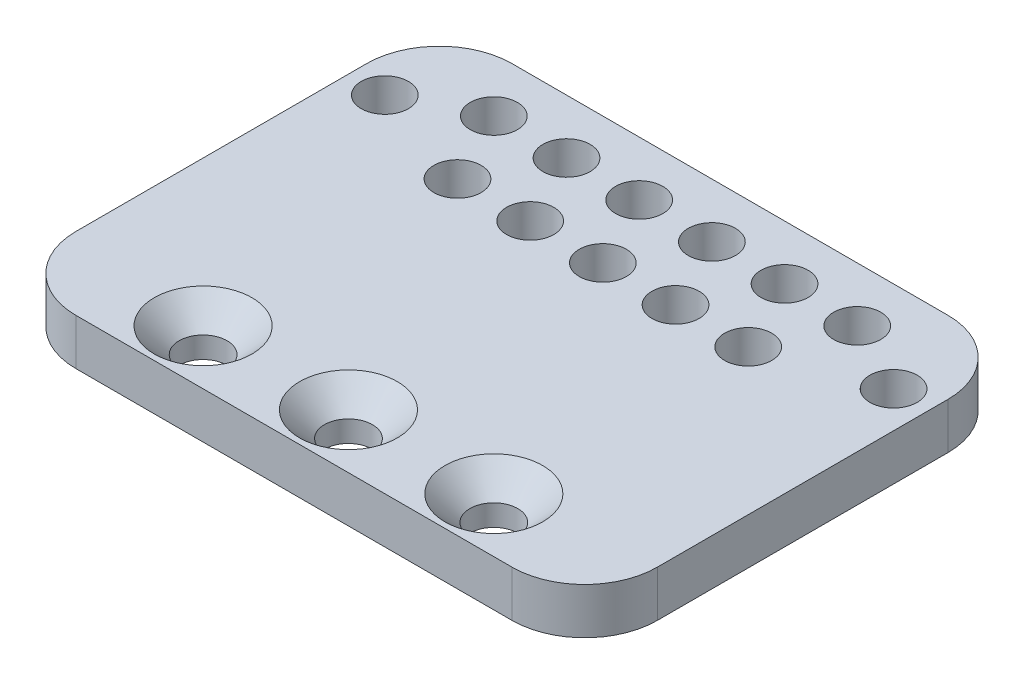
SolidWorks part; units mm, degrees
ref_plane "Front Plane" through (0, 0, 0) normal (0, 0, 1) x (1, 0, 0)
ref_plane "Top Plane" through (0, 0, 0) normal (0, 1, 0) x (1, 0, 0)
ref_plane "Right Plane" through (0, 0, 0) normal (1, 0, 0) x (0, 0, -1)
sketch "Sketch1" plane through (0, 0, 0) normal (0, 1, 0) x (1, 0, 0)
  line L1 (0, 0) -> (80, 0)
  line L2 (0, 0) -> (0, 60)
  line L3 (0, 60) -> (80, 60)
  line L4 (80, 0) -> (80, 60)
  line L5 (0, 0) -> (80, 60) construction
  line L6 (0, 60) -> (80, 0) construction
  line L8 (0, 37.5) -> (80, 37.5) construction
  line L9 (0, 17.5) -> (80, 17.5) construction
  line L10 (35, 52.5) -> (45, 52.5) construction
  line L11 (40, 42.5) -> (40, 52.5) construction
  line L12 (40, 47.5) -> (80, 47.5) construction
  line L13 (40, 47.5) -> (0, 47.5) construction
  circle A0 centre (40, 7.5) radius 3.1
  circle A1 centre (20, 7.5) radius 3.1
  circle A2 centre (60, 7.5) radius 3.1
  circle A5 centre (25, 27.35) radius 3.1 construction
  circle A7 centre (55, 27.35) radius 3.1 construction
  circle A8 centre (35, 52.5) radius 3.25
  circle A9 centre (45, 52.5) radius 3.25
  circle A10 centre (25, 52.5) radius 3.25
  circle A11 centre (30, 42.5) radius 3.25
  circle A12 centre (40, 42.5) radius 3.25
  circle A13 centre (50, 42.5) radius 3.25
  circle A14 centre (20, 42.5) radius 3.25
  circle A15 centre (15, 52.5) radius 3.25
  circle A16 centre (55, 52.5) radius 3.25
  circle A17 centre (65, 52.5) radius 3.25
  circle A18 centre (60, 42.5) radius 3.25
  circle A19 centre (75, 47.5) radius 3.25
  circle A20 centre (5, 47.5) radius 3.25
  point P4 (40, 30)
  point P12 (0, 0)
  point P13 (0, 0)
  point P48 (40, 52.5)
  dimension "D5" = 6.2
  dimension "D7" = 19.85
  dimension "D13" = 6.5
  dimension "D1" = 80
  dimension "D2" = 60
  dimension "D3" = 20
  dimension "D4" = 20
  dimension "D6" = 7.5
  dimension "D8" = 25
  dimension "D9" = 25
  dimension "D10" = 10
  dimension "D11" = 30
  dimension "D12" = 10
  dimension "D14" = 10
  dimension "D15" = 7.5
  dimension "D16" = 10
  dimension "D17" = 10
  dimension "D18" = 10
  dimension "D19" = 10
  dimension "D20" = 10
  dimension "D21" = 10
  dimension "D22" = 10
  dimension "D23" = 10
  dimension "D24" = 5
  dimension "D25" = 5
extrude "Boss-Extrude1" add sketch "Sketch1" along normal blind 6.35
fillet "Fillet1" radius 10 4 edges at (0, 3.175, -60) (80, 3.175, -60) (80, 3.175, 0) (0, 3.175, 0)
hole_wizard "CSK for M6 SFHCS1" positions "Sketch2" profile "Sketch3" countersink size "M6" standard "Autoliv NAM Metric" end condition up to next
sketch "Sketch2" plane through (0, 6.35, 0) normal (0, 1, 0) x (1, 0, 0)
  point P0 (20, 7.5)
  point P3 (40, 7.5)
  point P6 (60, 7.5)
sketch "Sketch3" plane through (20, 6.35, -7.5) normal (1, 0, 0) x (0, 0, 1)
  line L0 (0, 0) -> (0, 6.35)
  line L1 (0, 6.35) -> (3.3, 6.35)
  line L2 (3.3, 6.35) -> (3.3, 3.42)
  line L3 (3.3, 3.42) -> (6.72, 0)
  line L5 (6.72, 0) -> (0, 0)
  line L6 (-3.3, 3.42) -> (-6.72, 0) construction
  line L11 (0, -6.35) -> (0, 107.95) construction
  dimension "Thru Hole Dia." = 6.6
  dimension "Thru Hole Depth" = 6.35
  dimension "Near C'Sink Dia." = 13.44
  dimension "Near C'Sink Angle" = 90
